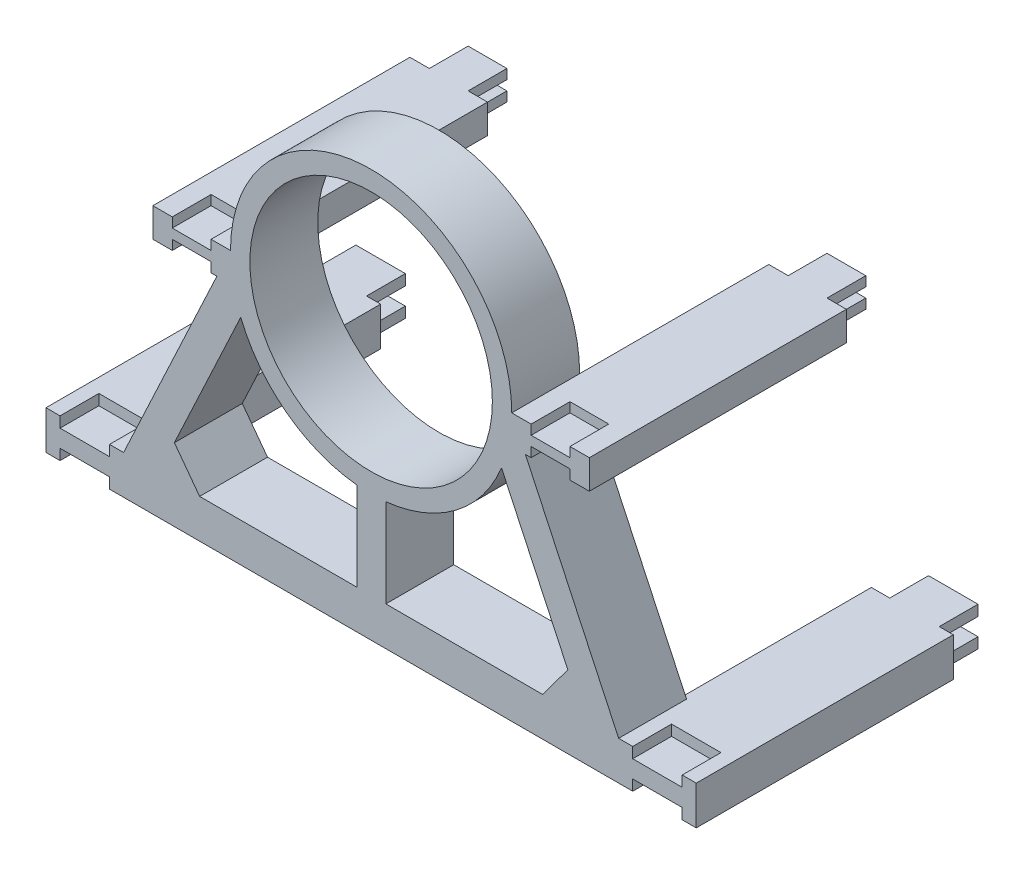
SolidWorks part; units mm, degrees
material "1023 Carbon Steel Sheet (SS)"
ref_plane "Ön Düzlem" through (0, 0, 0) normal (0, 0, 1) x (1, 0, 0)
ref_plane "Üst Düzlem" through (0, 0, 0) normal (0, 1, 0) x (1, 0, 0)
ref_plane "Sağ Düzlem" through (0, 0, 0) normal (1, 0, 0) x (0, 0, -1)
sketch "Sketch1" plane through (0, 0, 0) normal (0, 0, 1) x (1, 0, 0)
  line L0 (-72.5, 0) -> (-127.6009, -117.745)
  line L1 (-127.6009, -117.745) -> (-109.6009, -117.745)
  line L2 (-109.6009, -117.745) -> (-67.2156, -27.1719)
  line L3 (-109.6009, -117.745) -> (109.6009, -117.745)
  line L4 (0, -117.745) -> (0, -137.745)
  line L5 (167.6009, -137.745) -> (-167.6009, -137.745)
  line L6 (-167.6009, -137.745) -> (-167.6009, -117.745)
  line L7 (-167.6009, -117.745) -> (-127.6009, -117.745)
  line L8 (-7.4061, -72.1207) -> (-7.4061, -117.745)
  line L10 (7.5939, -72.1012) -> (7.5939, -117.745)
  line L11 (-101.4175, -100.2578) -> (-88.4083, -117.745)
  line L12 (-101.4175, -100.2578) -> (-119.4175, -100.2578)
  line L13 (101.4175, -100.2578) -> (119.4175, -100.2578)
  line L14 (101.4175, -100.2578) -> (88.4083, -117.745)
  line L15 (109.6009, -117.745) -> (67.2156, -27.1719)
  line L16 (72.5, 0) -> (127.6009, -117.745)
  line L17 (167.6009, -137.745) -> (167.6009, -117.745)
  line L18 (167.6009, -117.745) -> (127.6009, -117.745)
  line L19 (127.6009, -117.745) -> (109.6009, -117.745)
  line L20 (7.4061, -72.1207) -> (7.4061, -117.745)
  circle A0 centre (0, 0) radius 62.5
  circle A1 centre (0, 0) radius 72.5
  dimension "D1" = 125
  dimension "D2" = 10
  dimension "D3" = 100
  dimension "D4" = 130
  dimension "D5" = 18
  dimension "D6" = 40
  dimension "D7" = 167.6009
  dimension "D8" = 15
  dimension "D9" = 20
  dimension "D10" = 45.6243
  dimension "D11" = 21.7955
  dimension "D12" = 17.4872
extrude "Boss-Extrude8" add sketch "Sketch1" along normal blind 35 contours A1 A0 | A1 L0 L12 L2 | L2 L12 L0 L1 | L11 L2 L3 | L7 L6 L5 L4 L3 L1 | L18 L19 L3 L4 L5 L17 | L3 L15 L14 | L19 L16 L13 L15 | A1 L15 L13 L16
sketch "Sketch2" plane through (0, -117.745, 0) normal (0, 1, 0) x (1, 0, 0)
  line L0 (-7.4061, 0) -> (-7.4061, -35)
  line L1 (-88.4083, -35) -> (88.4083, -35) construction
  line L2 (-7.4061, 0) -> (7.5939, 0)
  line L3 (7.5939, 0) -> (7.5939, -35)
  line L4 (7.5939, -35) -> (-7.4061, -35)
extrude "Boss-Extrude9" add sketch "Sketch2" along normal up to surface (45.6243 mm away)
ref_plane "Plane3" through (72.5, 0, 0) normal (1, 0, 0) x (0, 0, -1)
sketch "Sketch6" plane through (72.5, 0, 0) normal (1, 0, 0) x (0, 0, -1)
  line L0 (80.1625, 0) -> (-80.1625, 0) construction
  line L1 (-35, 0) -> (0, 0)
  line L2 (-35, 0) -> (-35, -15)
  line L3 (-35, -15) -> (0, -15)
  line L4 (0, 0) -> (0, -15)
  line L5 (-35, 72.5) -> (-35, 0) construction
  line L6 (0, 72.5) -> (0, -72.5) construction
  dimension "D1" = 35
  dimension "D2" = 15
ref_plane "Plane5" through (-72.5, 0, 0) normal (1, 0, 0) x (0, 0, -1)
sketch "Sketch10" plane through (-72.5, 0, 0) normal (1, 0, 0) x (0, 0, -1)
  line L0 (-35, 0) -> (-35, -117.745) construction
  line L1 (0, 0) -> (-35, 0)
  line L2 (0, 0) -> (0, -15)
  line L3 (0, -15) -> (-35, -15)
  line L4 (-35, 0) -> (-35, -15)
  dimension "D1" = 35
  dimension "D2" = 15
extrude "Boss-Extrude12" add sketch "Sketch10" against normal blind 40
extrude "Boss-Extrude10" add sketch "Sketch6" along normal blind 40
sketch "Sketch12" plane through (0, 0, 0) normal (0, 0, -1) x (-1, 0, 0)
  line L4 (-167.6009, -137.745) -> (-125.3715, -137.745)
  line L5 (-167.6009, -137.745) -> (167.6009, -137.745) construction
  line L6 (-125.3715, -137.745) -> (-125.3715, -117.745)
  line L7 (-127.6009, -117.745) -> (-109.6009, -117.745) construction
  line L8 (-125.3715, -117.745) -> (-167.6009, -117.745)
  line L9 (-167.6009, -117.745) -> (-167.6009, -137.745)
  line L14 (127.6009, -117.745) -> (127.6009, -137.745)
  line L15 (127.6009, -137.745) -> (167.6009, -137.745)
  line L16 (167.6009, -137.745) -> (167.6009, -117.745)
  line L17 (167.6009, -117.745) -> (127.6009, -117.745)
  line L18 (-112.5, 0) -> (-72.5, 0)
  line L19 (-72.5, 0) -> (-72.5, -15)
  line L20 (-72.5, -15) -> (-112.5, -15)
  line L21 (-112.5, -15) -> (-112.5, 0)
  line L23 (112.5, 0) -> (72.5042, 0)
  line L24 (112.5, 0) -> (112.5, -15)
  line L25 (112.5, -15) -> (72.5042, -15)
  line L26 (72.5042, 0) -> (72.5042, -15)
  dimension "D1" = 20
  dimension "D2" = 42.2294
  dimension "D3" = 15
  dimension "D4" = 40
  dimension "D5" = 15
  dimension "D6" = 39.9958
extrude "Boss-Extrude13" add sketch "Sketch12" along normal blind 97.5
sketch "Sketch13" plane through (0, 0, 35) normal (0, 0, 1) x (1, 0, 0)
  line L0 (-112.5, 0) -> (-72.5, 0) construction
  line L1 (-102.5, 0) -> (-82.5, 0)
  line L2 (-102.5, 0) -> (-102.5, -5)
  line L3 (-102.5, -5) -> (-82.5, -5)
  line L4 (-82.5, 0) -> (-82.5, -5)
  line L5 (-112.5, -15) -> (-79.5195, -15) construction
  line L6 (-102.5, -15) -> (-82.5, -15)
  line L7 (-102.5, -15) -> (-102.5, -10)
  line L8 (-102.5, -10) -> (-82.5, -10)
  line L9 (-82.5, -15) -> (-82.5, -10)
  line L10 (112.5, 0) -> (72.5, 0) construction
  line L11 (82.5, 0) -> (102.5, 0)
  line L12 (82.5, 0) -> (82.5, -5)
  line L13 (82.5, -5) -> (102.5, -5)
  line L14 (102.5, 0) -> (102.5, -5)
  line L15 (112.5, -15) -> (79.5195, -15) construction
  line L16 (82.5, -15) -> (102.5, -15)
  line L17 (82.5, -15) -> (82.5, -10)
  line L18 (82.5, -10) -> (102.5, -10)
  line L19 (102.5, -15) -> (102.5, -10)
  line L20 (167.6009, -117.745) -> (127.6009, -117.745) construction
  line L21 (134.8509, -117.745) -> (160.3509, -117.745)
  line L22 (134.8509, -117.745) -> (134.8509, -123.245)
  line L23 (134.8509, -123.245) -> (160.3509, -123.245)
  line L24 (160.3509, -117.745) -> (160.3509, -123.245)
  line L25 (167.6009, -137.745) -> (-167.6009, -137.745) construction
  line L26 (134.8509, -137.745) -> (160.3509, -137.745)
  line L27 (134.8509, -137.745) -> (134.8509, -132.245)
  line L28 (134.8509, -132.245) -> (160.3509, -132.245)
  line L29 (160.3509, -137.745) -> (160.3509, -132.245)
  line L30 (-167.6009, -117.745) -> (-127.6009, -117.745) construction
  line L31 (-160.3509, -117.745) -> (-134.8509, -117.745)
  line L32 (-160.3509, -117.745) -> (-160.3509, -123.245)
  line L33 (-160.3509, -123.245) -> (-134.8509, -123.245)
  line L34 (-134.8509, -117.745) -> (-134.8509, -123.245)
  line L35 (-102.5, 0) -> (-112.5, 0)
  line L36 (-160.3509, -137.745) -> (-134.8509, -137.745)
  line L37 (-160.3509, -137.745) -> (-160.3509, -132.245)
  line L38 (-160.3509, -132.245) -> (-134.8509, -132.245)
  line L39 (-134.8509, -137.745) -> (-134.8509, -132.245)
  point P46 (0, 0)
  line M8 (-112.5, -15) -> (-79.5195, -15)
  line M12 (-167.6009, -137.745) -> (167.6009, -137.745)
  dimension "D1" = 20
  dimension "D2" = 10
  dimension "D3" = 5
  dimension "D4" = 5
  dimension "D5" = 20
  dimension "D6" = 10
  dimension "D7" = 10
  dimension "D8" = 20
  dimension "D9" = 5
  dimension "D10" = 5
  dimension "D11" = 10
  dimension "D12" = 20
  dimension "D13" = 7.25
  dimension "D14" = 7.25
  dimension "D15" = 25.5
  dimension "D16" = 25.5
  dimension "D17" = 5.5
  dimension "D18" = 5.5
  dimension "D19" = 25.5
  dimension "D20" = 25.5
  dimension "D21" = 7.25
  dimension "D22" = 5.5
  dimension "D23" = 5.5
  dimension "D24" = 7.25
extrude "Cut-Extrude1" cut sketch "Sketch13" against normal blind 20 contours L9 L8 L7 M8 | L39 L38 L37 M12 | L1 L4 L3 L2 | L13 L14 L11 L12 | L18 L19 L16 L17 | L21 L24 L23 L22 | L28 L29 L26 L27 | L33 L34 L31 L32
sketch "Sketch14" plane through (0, 0, -97.5) normal (0, 0, -1) x (-1, 0, 0)
  line L0 (-72.5, 0) -> (-112.5, 0) construction
  line L1 (-102.5, 0) -> (-82.5, 0)
  line L2 (-102.5, 0) -> (-102.5, -5)
  line L3 (-102.5, -5) -> (-82.5, -5)
  line L4 (-82.5, 0) -> (-82.5, -5)
  line L5 (112.5, 0) -> (72.5042, 0) construction
  line L6 (-102.5, -15) -> (-82.5, -15)
  line L7 (-102.5, -15) -> (-102.5, -10)
  line L8 (-102.5, -10) -> (-82.5, -10)
  line L9 (-82.5, -15) -> (-82.5, -10)
  line L10 (82.5, 0) -> (102.5, 0)
  line L11 (82.5, 0) -> (82.5, -5)
  line L12 (82.5, -5) -> (102.5, -5)
  line L13 (102.5, 0) -> (102.5, -5)
  line L14 (72.5042, -15) -> (112.5, -15) construction
  line L15 (82.5, -15) -> (102.5, -15)
  line L16 (82.5, -15) -> (82.5, -10)
  line L17 (82.5, -10) -> (102.5, -10)
  line L18 (102.5, -15) -> (102.5, -10)
  line L19 (167.6009, -117.745) -> (127.6009, -117.745) construction
  line L20 (134.8509, -117.745) -> (160.3509, -117.745)
  line L21 (134.8509, -117.745) -> (134.8509, -123.245)
  line L22 (134.8509, -123.245) -> (160.3509, -123.245)
  line L23 (160.3509, -117.745) -> (160.3509, -123.245)
  line L24 (-167.6009, -137.745) -> (167.6009, -137.745) construction
  line L25 (134.8509, -137.745) -> (160.3509, -137.745)
  line L26 (134.8509, -137.745) -> (134.8509, -132.245)
  line L27 (134.8509, -132.245) -> (160.3509, -132.245)
  line L28 (160.3509, -137.745) -> (160.3509, -132.245)
  line L29 (112.5, -15) -> (112.5, 0) construction
  line L30 (-160.3509, -117.745) -> (-134.8509, -117.745)
  line L31 (-160.3509, -117.745) -> (-160.3509, -123.245)
  line L32 (-160.3509, -123.245) -> (-134.8509, -123.245)
  line L33 (-134.8509, -117.745) -> (-134.8509, -123.245)
  line L34 (-160.3509, -137.745) -> (-134.8509, -137.745)
  line L35 (-160.3509, -137.745) -> (-160.3509, -132.245)
  line L36 (-160.3509, -132.245) -> (-134.8509, -132.245)
  line L37 (-134.8509, -137.745) -> (-134.8509, -132.245)
  line L38 (-112.5, 0) -> (-112.5, -15) construction
  dimension "D1" = 7.25
  dimension "D2" = 25.5
  dimension "D3" = 25.5
  dimension "D4" = 5.5
  dimension "D5" = 5.5
  dimension "D6" = 5.5
  dimension "D7" = 25.5
  dimension "D8" = 7.25
  dimension "D9" = 7.25
  dimension "D10" = 25.5
  dimension "D11" = 5.5
  dimension "D12" = 10
  dimension "D13" = 10
  dimension "D14" = 20
  dimension "D15" = 20
  dimension "D16" = 5
  dimension "D17" = 5
  dimension "D18" = 5
  dimension "D19" = 20
  dimension "D20" = 20
  dimension "D21" = 10
  dimension "D22" = 5
extrude "Boss-Extrude14" add sketch "Sketch14" along normal blind 20
